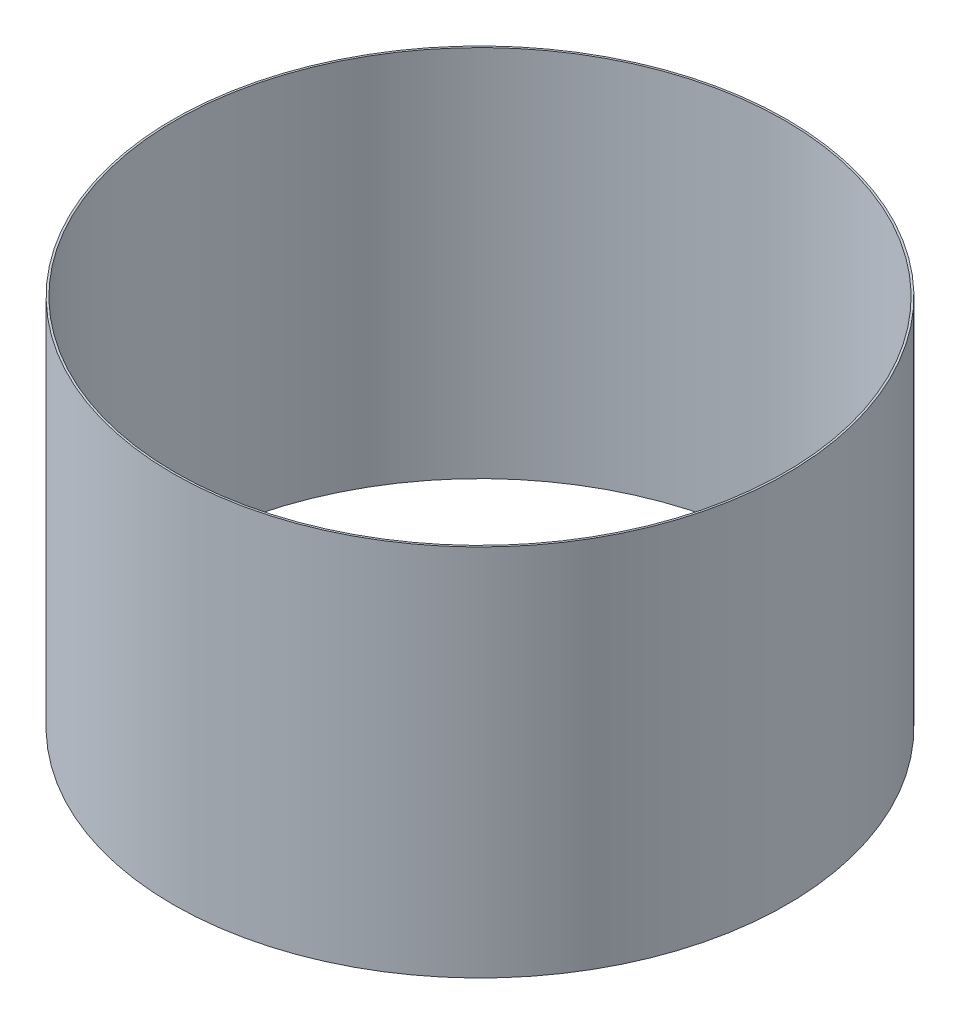
SolidWorks part; units mm, degrees
other "Markup1"
sketch "Sketch4" plane through (125.2538, 0, -125.2537) normal (0.1, -0.9946, -0.0262) x (-0.5456, -0.0768, 0.8345)
ref_plane "Front" through (0, 0, 0) normal (0, 0, 1) x (1, 0, 0)
ref_plane "Top" through (0, 0, 0) normal (0, 1, 0) x (1, 0, 0)
ref_plane "Right" through (0, 0, 0) normal (1, 0, 0) x (0, 0, -1)
sketch "Sketch1" plane through (0, 0, 0) normal (0, 1, 0) x (1, 0, 0)
  circle A0 centre (0, 0) radius 125.2537
  dimension "D1" = 250.5075
extrude "Boss-Extrude1" add sketch "Sketch1" along normal blind 152.4
sketch "Sketch3" plane through (0, 0, 0) normal (0, -1, 0) x (1, 0, 0)
  circle A0 centre (0, 0) radius 124.46
  dimension "D1" = 248.92
extrude "Cut-Extrude1" cut sketch "Sketch3" against normal through all
